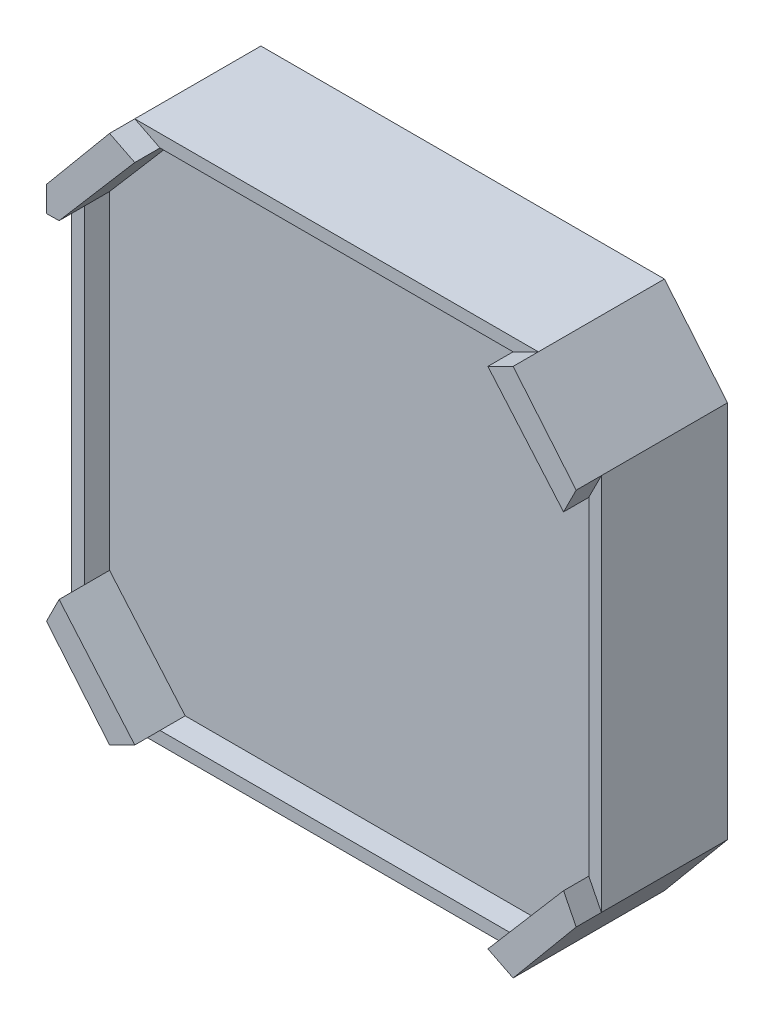
SolidWorks part; units mm, degrees
ref_plane "Alzado" through (0, 0, 0) normal (0, 0, 1) x (1, 0, 0)
ref_plane "Planta" through (0, 0, 0) normal (0, 1, 0) x (1, 0, 0)
ref_plane "Vista lateral" through (0, 0, 0) normal (1, 0, 0) x (0, 0, -1)
sketch "Croquis2" plane through (0, 0, 0) normal (0, 0, 1) x (1, 0, 0)
  line L0 (0, 21) -> (0, 32.1176) construction
  line L1 (-16, 21) -> (16, 21)
  line L2 (-21, 15) -> (-21, -15)
  line L3 (-16, -21) -> (16, -21)
  line L4 (21, 15) -> (21, -15)
  line L5 (-21, 21) -> (21, -21) construction
  line L6 (-21, -21) -> (21, 21) construction
  line L7 (0, 32.1176) -> (-16, 32.1176) construction
  line L8 (-16, 21) -> (-16, 15) construction
  line L9 (-16, 21) -> (-21, 15)
  line L10 (16, 21) -> (21, 15)
  line L11 (0, 0) -> (3.8385, 0) construction
  line L12 (16, -21) -> (21, -15)
  line L13 (-16, -21) -> (-21, -15)
  point P0 (0, 0)
  dimension "D1" = 42
  dimension "D2" = 42
extrude "Saliente-Extruir1" add sketch "Croquis2" along normal blind 10
sketch "Croquis3" plane through (0, 0, 10) normal (0, 0, 1) x (1, 0, 0)
  line L0 (-20, 8.0237) -> (-14, 8.0237) construction
  line L1 (-14, 20) -> (14, 20)
  line L2 (-20, 13.0049) -> (-20, -13.0049)
  line L3 (-14, -20) -> (14, -20)
  line L4 (20, 13.0049) -> (20, -13.0049)
  line L5 (-20, 20) -> (20, -20) construction
  line L6 (-20, -20) -> (20, 20) construction
  line L7 (-14, 20) -> (-14, 14) construction
  line L8 (-14, 20) -> (-20, 13.0049)
  line L9 (0, 0) -> (0, 5.1257) construction
  line L10 (0, 0) -> (6.8139, 0) construction
  line L11 (14, 20) -> (20, 13.0049)
  line L12 (14, -20) -> (20, -13.0049)
  line L13 (-14, -20) -> (-20, -13.0049)
  point P0 (0, 0)
  dimension "D1" = 40
  dimension "D2" = 40
extrude "Cortar-Extruir1" cut sketch "Croquis3" against normal blind 2
sketch "Croquis4" plane through (0, 0, 10) normal (0, 0, 1) x (1, 0, 0)
  line L0 (-16, 21) -> (-21, 15)
  line L1 (-21, 15) -> (-21, 12.992)
  line L2 (-21, 15) -> (-21, -15) construction
  line L3 (-21, 12.992) -> (-20, 13.0049)
  line L4 (-20, 13.0049) -> (-14, 20)
  line L5 (-14, 20) -> (-16, 21)
  line L6 (16, 21) -> (21, 15)
  line L7 (21, 15) -> (20, 13.0049)
  line L8 (20, 13.0049) -> (14, 20)
  line L9 (14, 20) -> (16, 21)
  line L10 (16, 21) -> (16.1281, 21.0712)
  line L11 (20, -13.0049) -> (14, -20)
  line L12 (14, -20) -> (16, -21)
  line L13 (16, -21) -> (21, -15)
  line L14 (21, -15) -> (20, -13.0049)
  line L15 (-14, -20) -> (-20, -13.0049)
  line L16 (-20, -13.0049) -> (-21, -15)
  line L17 (-21, -15) -> (-16, -21)
  line L18 (-16, -21) -> (-14, -20)
  line M8 (-14, -20) -> (-20, -13.0049)
  line M11 (-21, -15) -> (-16, -21)
extrude "Saliente-Extruir2" add sketch "Croquis4" along normal blind 2 contours L18 L16 M11 M8 | L4 L5 L0 L1 L3 | L6 L7 L8 L9 | L13 L14 L11 L12
sketch "Croquis5" plane through (0, 0, 0) normal (0, 0, -1) x (-1, 0, 0)
  line L0 (0, 0) -> (15.5, 0) construction
  line L1 (0, 0) -> (0, 7.4677) construction
  line L2 (15.5, 0) -> (15.5, 15.5) construction
  circle A0 centre (15.5, 15.5) radius 1.4
  circle A1 centre (-15.5, 15.5) radius 1.4
  circle A2 centre (15.5, -15.5) radius 1.4
  circle A3 centre (-15.5, -15.5) radius 1.4
  circle A4 centre (0, 0) radius 2.5
  dimension "D1" = 2.8
  dimension "D2" = 5
extrude "Cortar-Extruir2" cut sketch "Croquis5" against normal blind 5
sketch "Croquis6" plane through (0, 0, 0) normal (0, 0, -1) x (-1, 0, 0)
  circle A0 centre (0, 0) radius 15
  dimension "D1" = 30
extrude "Cortar-Extruir3" cut sketch "Croquis6" against normal blind 1
sketch "Croquis7" plane through (0, 0, 1) normal (0, 0, -1) x (-1, 0, 0)
  circle A0 centre (0, 0) radius 11
  circle A1 centre (0, 0) radius 4
  dimension "D1" = 22
  dimension "D2" = 8
extrude "Saliente-Extruir3" add sketch "Croquis7" along normal blind 3
